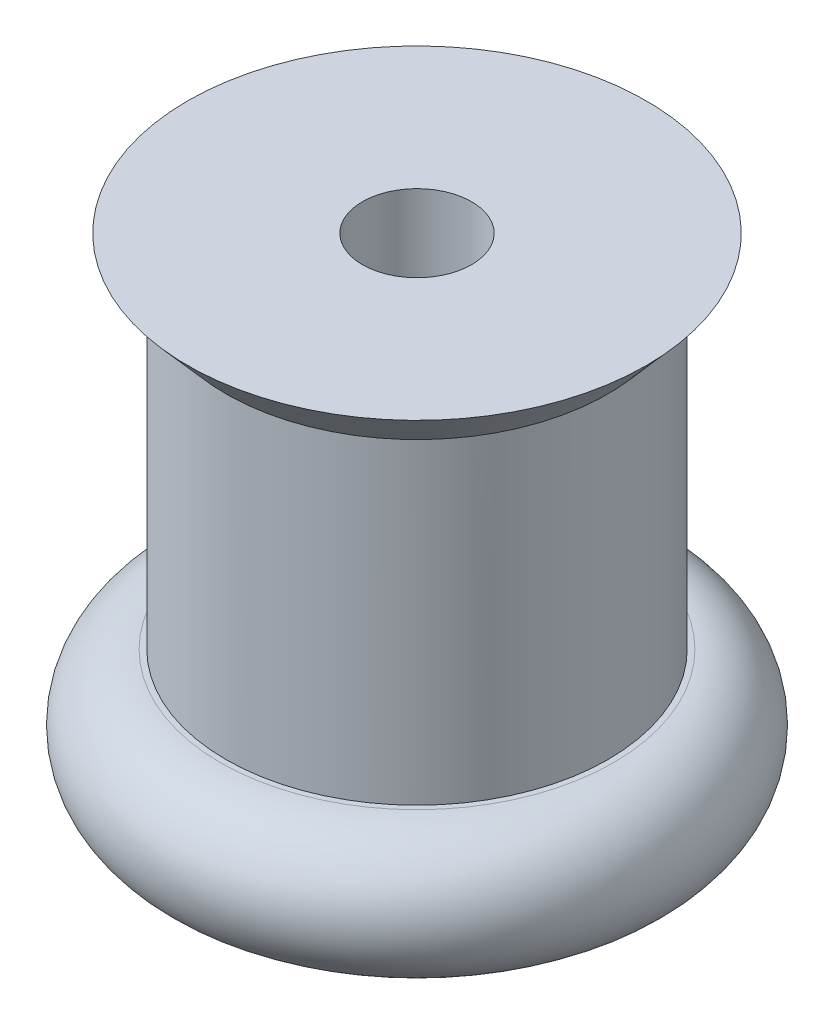
SolidWorks part; units mm, degrees
material "ABS"
ref_plane "Front Plane" through (0, 0, 0) normal (0, 0, 1) x (1, 0, 0)
ref_plane "Top Plane" through (0, 0, 0) normal (0, 1, 0) x (1, 0, 0)
ref_plane "Right Plane" through (0, 0, 0) normal (1, 0, 0) x (0, 0, -1)
sketch "Sketch1" plane through (0, 0, 0) normal (0, 1, 0) x (1, 0, 0)
  circle A0 centre (0, 0) radius 12
  circle A1 centre (0, 0) radius 2.5
extrude "Boss-Extrude1" add sketch "Sketch1" along normal blind 6
sketch "Sketch2" plane through (0, 6, 0) normal (0, 1, 0) x (1, 0, 0)
  circle A0 centre (0, 0) radius 2.5
  circle A1 centre (0, 0) radius 8.75
extrude "Boss-Extrude2" add sketch "Sketch2" along normal blind 14.5
sketch "Sketch3" plane through (0, 20.5, 0) normal (0, 1, 0) x (1, 0, 0)
  circle A0 centre (0, 0) radius 2.5
  circle A1 centre (0, 0) radius 10.5
extrude "Boss-Extrude3" add sketch "Sketch3" along normal blind 2
sketch "Sketch5" plane through (0, 0, 0) normal (0, 0, 1) x (1, 0, 0)
  line L0 (-10.5, 22.5) -> (-8.75, 20.5)
  line L1 (-10.5, 20.5) -> (10.5, 20.5) construction
  line L2 (-10.5, 22.5) -> (-10.5, 20.5) construction
  line L3 (-10.5, 20.5) -> (-8.75, 20.5)
  line L4 (-10.5, 22.5) -> (-10.5, 20.5)
sweep "Cut-Sweep3" cut profiles "Sketch5" path edge at (0, 20.5, 8.75)
sketch "Sketch6" plane through (0, 0, 0) normal (0, 0, 1) x (1, 0, 0)
  line L0 (-12, 3) -> (-12, 6)
  line L2 (-12, 6) -> (-9, 6)
  arc A0 (-9, 6) -> (-12, 3) centre (-9, 3) ccw
sweep "Cut-Sweep4" cut profiles "Sketch6" path edge at (0, 6, 12)
sketch "Sketch7" plane through (0, 0, 0) normal (0, 0, 1) x (1, 0, 0)
  line L1 (-12, 3) -> (12, 3) construction
  line L2 (-9, 0) -> (-12, 0)
  line L3 (-12, 0) -> (-12, 3)
  arc A0 (-12, 3) -> (-9, 0) centre (-9, 3) ccw
sweep "Cut-Sweep5" cut profiles "Sketch7" path edge at (0, 0, 12)
